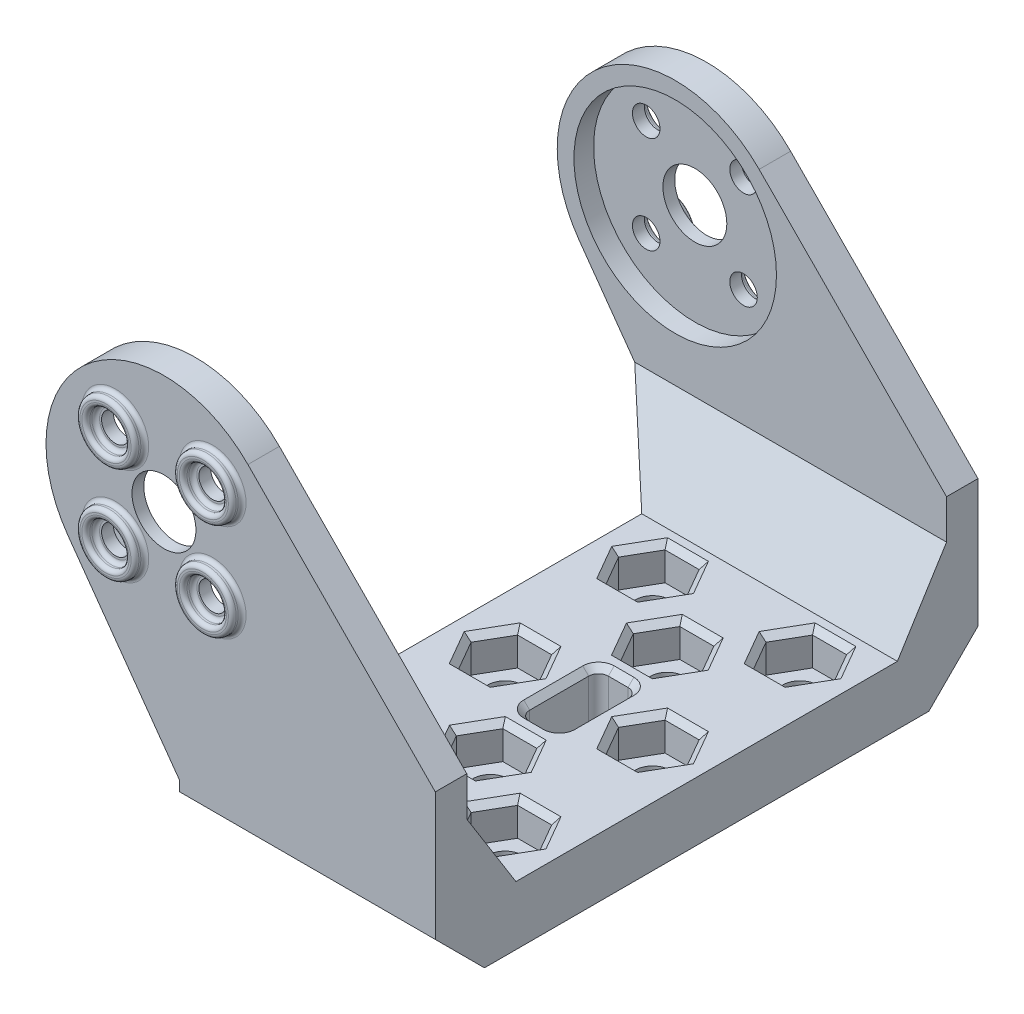
SolidWorks part; units mm, degrees
ref_plane "Спереди" through (0, 0, 0) normal (0, 0, 1) x (1, 0, 0)
ref_plane "Сверху" through (0, 0, 0) normal (0, 1, 0) x (1, 0, 0)
ref_plane "Справа" through (0, 0, 0) normal (1, 0, 0) x (0, 0, -1)
sketch "Эскиз1" plane through (0, 0, 0) normal (0, 0, 1) x (1, 0, 0)
  line L0 (0, 0) -> (0, -64.8775) construction
  line L1 (-4.9497, 4.9497) -> (4.9497, 4.9497) construction
  line L2 (-4.9497, 4.9497) -> (-4.9497, -4.9497) construction
  line L3 (-4.9497, -4.9497) -> (4.9497, -4.9497) construction
  line L4 (4.9497, 4.9497) -> (4.9497, -4.9497) construction
  line L5 (-4.9497, 4.9497) -> (4.9497, -4.9497) construction
  line L6 (-4.9497, -4.9497) -> (4.9497, 4.9497) construction
  line L7 (0, -64.8775) -> (14.6, -64.8775) construction
  line L8 (24.6, -34.8775) -> (4.6, -34.8775) construction
  line L9 (24.6, -34.8775) -> (24.6, -74.8775) construction
  line L10 (4.6, -34.8775) -> (4.6, -74.8775) construction
  line L11 (4.6, -74.8775) -> (24.6, -74.8775) construction
  line L12 (14.6, -73.302) -> (14.6, -29.9429) construction
  line L13 (2.6, -28.8775) -> (26.6, -28.8775) construction
  line L14 (2.6, -28.8775) -> (2.6, -48.8775) construction
  line L15 (2.6, -48.8775) -> (26.6, -48.8775) construction
  line L16 (26.6, -28.8775) -> (26.6, -48.8775) construction
  line L17 (1.6, -28.8775) -> (1.6, -22.8775)
  line L18 (1.6, -28.8775) -> (27.6, -28.8775)
  line L19 (27.6, -28.8775) -> (27.6, -10.8775)
  line L20 (27.6, -10.8775) -> (8.5399, 8.4303)
  line L21 (1.6, -22.8775) -> (-9.7631, -6.9772)
  circle A0 centre (0, 0) radius 3.25
  circle A1 centre (-4.9497, 4.9497) radius 1.4
  circle A2 centre (4.9497, 4.9497) radius 1.4
  circle A3 centre (4.9497, -4.9497) radius 1.4
  circle A4 centre (-4.9497, -4.9497) radius 1.4
  circle A5 centre (0, 0) radius 10 construction
  circle A6 centre (7.1, -37.3775) radius 1 construction
  arc A7 (8.5399, 8.4303) -> (-9.7631, -6.9772) centre (0, 0) ccw
  circle A11 centre (14.6, -64.8775) radius 10 construction
  circle A12 centre (14.6, -37.1275) radius 1 construction
  circle A13 centre (21.6, -44.1275) radius 1 construction
  circle A14 centre (7.6, -44.1275) radius 1 construction
  point P3 (0, 0)
  point P50 (32.6, -34.8775)
  dimension "D1" = 6.5
  dimension "D3" = 2.8
  dimension "D6" = 20
  dimension "D9" = 2
  dimension "D15" = 6
  dimension "D16" = 10
  dimension "D17" = 14
  dimension "D21" = 26
  dimension "D22" = 6
  dimension "D20" = 24
  dimension "D2" = 14
  dimension "D4" = 66.5
  dimension "D5" = 14.6
  dimension "D7" = 27.5
  dimension "D8" = 7.5
  dimension "D10" = 18
  dimension "D12" = 30
  dimension "D13" = 20
  dimension "D14" = 40
  dimension "D18" = 24
  dimension "D19" = 7
  dimension "D24" = 27.75
  dimension "D25" = 7
  dimension "D26" = 7
extrude "Бобышка-Вытянуть1" add sketch "Эскиз1" along normal blind 3.2
sketch "Эскиз2" plane through (0, 0, 3.2) normal (0, 0, 1) x (1, 0, 0)
  line L1 (27.6, -28.8775) -> (1.6, -28.8775)
  line L2 (27.6, -28.8775) -> (27.6, -22.8775)
  line L3 (27.6, -22.8775) -> (1.6, -22.8775)
  line L4 (1.6, -28.8775) -> (1.6, -22.8775)
extrude "Бобышка-Вытянуть2" add sketch "Эскиз2" along normal blind 48.8
sketch "Эскиз3" plane through (0, 0, 52) normal (0, 0, 1) x (1, 0, 0)
  line L5 (1.6, -28.8775) -> (27.6, -28.8775)
  line L6 (1.6, -22.8775) -> (1.6, -28.8775)
  line L7 (-9.7631, -6.9772) -> (1.6, -22.8775)
  line L8 (27.6, -10.8775) -> (8.5399, 8.4303)
  line L9 (27.6, -28.8775) -> (27.6, -10.8775)
  line L10 (1.6, -28.8775) -> (27.6, -28.8775)
  line L11 (1.6, -22.8775) -> (1.6, -28.8775)
  line L12 (-9.7631, -6.9772) -> (1.6, -22.8775)
  line L13 (27.6, -10.8775) -> (8.5399, 8.4303)
  line L14 (27.6, -28.8775) -> (27.6, -10.8775)
  circle A0 centre (-4.9497, 4.9497) radius 1.4 construction
  arc A1 (8.5399, 8.4303) -> (-9.7631, -6.9772) centre (0, 0) ccw
  arc A2 (8.5399, 8.4303) -> (-9.7631, -6.9772) centre (0, 0) ccw
  circle A3 centre (0, 0) radius 3.25 construction
  circle A4 centre (-4.9497, -4.9497) radius 1.4 construction
  circle A5 centre (4.9497, -4.9497) radius 1.4 construction
  circle A6 centre (4.9497, 4.9497) radius 1.4 construction
  circle A7 centre (-4.9497, 4.9497) radius 1.4
  circle A8 centre (0, 0) radius 3.25
  circle A9 centre (-4.9497, -4.9497) radius 1.4
  circle A10 centre (4.9497, -4.9497) radius 1.4
  circle A11 centre (4.9497, 4.9497) radius 1.4
  dimension "D1" = 0
extrude "Бобышка-Вытянуть3" add sketch "Эскиз3" along normal blind 3.2
sketch "Эскиз4" plane through (0, 0, 3.2) normal (0, 0, 1) x (1, 0, 0)
  circle A0 centre (0, 0) radius 10.3
  dimension "D1" = 20.6
extrude "Вырез-Вытянуть1" cut sketch "Эскиз4" against normal blind 2
sketch "Эскиз5" plane through (0, 0, 52) normal (0, 0, -1) x (-1, 0, 0)
  circle A0 centre (0, 0) radius 10.3 construction
  circle A1 centre (0, 0) radius 10.3
extrude "Вырез-Вытянуть2" cut sketch "Эскиз5" against normal blind 2
chamfer "Фаска1" distance 5 angle 45 2 edges at (14.6, -28.8775, 0) (14.6, -28.8775, 55.2)
sketch "Эскиз6" plane through (0, 0, 55.2) normal (0, 0, 1) x (1, 0, 0)
  circle A0 centre (-4.9497, 4.9497) radius 2
  circle A1 centre (-4.9497, 4.9497) radius 3
  circle A2 centre (-4.9497, -4.9497) radius 2
  circle A3 centre (4.9497, -4.9497) radius 2
  circle A4 centre (4.9497, -4.9497) radius 3
  circle A5 centre (-4.9497, -4.9497) radius 3
  circle A6 centre (4.9497, 4.9497) radius 2
  circle A7 centre (4.9497, 4.9497) radius 3
  dimension "D1" = 4
  dimension "D2" = 1
extrude "Бобышка-Вытянуть4" add sketch "Эскиз6" along normal blind 1
sketch "Эскиз7" plane through (0, 0, 0) normal (0, 0, -1) x (-1, 0, 0)
  circle A0 centre (4.9497, -4.9497) radius 3 construction
  circle A1 centre (4.9497, 4.9497) radius 3 construction
  circle A2 centre (-4.9497, 4.9497) radius 3 construction
  circle A3 centre (-4.9497, -4.9497) radius 3 construction
  circle A4 centre (4.9497, -4.9497) radius 3
  circle A5 centre (4.9497, 4.9497) radius 3
  circle A6 centre (-4.9497, 4.9497) radius 3
  circle A7 centre (-4.9497, -4.9497) radius 3
  circle A8 centre (4.9497, 4.9497) radius 2 construction
  circle A9 centre (-4.9497, 4.9497) radius 2 construction
  circle A10 centre (-4.9497, -4.9497) radius 2 construction
  circle A11 centre (4.9497, -4.9497) radius 2 construction
  circle A12 centre (4.9497, 4.9497) radius 2
  circle A13 centre (-4.9497, 4.9497) radius 2
  circle A14 centre (-4.9497, -4.9497) radius 2
  circle A15 centre (4.9497, -4.9497) radius 2
extrude "Бобышка-Вытянуть5" add sketch "Эскиз7" along normal blind 1
fillet "Скругление1" radius 0.4 32 edges at (7.9497, -4.9497, 0) (-1.9497, -4.9497, 0) (1.9497, -4.9497, -1) (2.9497, -4.9497, 0) (2.9497, -4.9497, -1) (-7.9497, -4.9497, -1) (-6.9497, -4.9497, 0) (-6.9497, -4.9497, -1) (-6.9497, 4.9497, 0) (-6.9497, 4.9497, -1) (-1.9497, 4.9497, 0) (-7.9497, 4.9497, -1) (7.9497, 4.9497, 0) (2.9497, 4.9497, 0) (2.9497, 4.9497, -1) (1.9497, 4.9497, -1) (-1.9497, 4.9497, 55.2) (-1.9497, -4.9497, 55.2) (7.9497, -4.9497, 55.2) (7.9497, 4.9497, 55.2) (-1.9497, 4.9497, 56.2) (-2.9497, 4.9497, 55.2) (-2.9497, 4.9497, 56.2) (6.9497, 4.9497, 55.2) (6.9497, 4.9497, 56.2) (7.9497, 4.9497, 56.2) (7.9497, -4.9497, 56.2) (-1.9497, -4.9497, 56.2) (-2.9497, -4.9497, 55.2) (-2.9497, -4.9497, 56.2) (6.9497, -4.9497, 55.2) (6.9497, -4.9497, 56.2)
sketch "Эскиз8" plane through (0, -22.8775, 0) normal (0, 1, 0) x (1, 0, 0)
  line L0 (-9.3037, -27.6) -> (38.3675, -27.6) construction
  line L1 (7.1, -12.6) -> (22.1, -12.6) construction
  line L2 (7.1, -12.6) -> (7.1, -42.6) construction
  line L3 (7.1, -42.6) -> (22.1, -42.6) construction
  line L4 (22.1, -12.6) -> (22.1, -42.6) construction
  line L5 (14.6, -8.2) -> (14.6, -47) construction
  line L7 (13.6, -31.6) -> (15.6, -31.6)
  line L8 (12.6, -30.6) -> (12.6, -24.6)
  line L9 (13.6, -23.6) -> (15.6, -23.6)
  line L10 (16.6, -30.6) -> (16.6, -24.6)
  line L11 (12.6, -31.6) -> (16.6, -23.6) construction
  line L12 (12.6, -23.6) -> (16.6, -31.6) construction
  circle A0 centre (7.1, -12.6) radius 1.75
  circle A1 centre (22.1, -12.6) radius 1.75
  circle A2 centre (22.1, -42.6) radius 1.75
  circle A3 centre (7.1, -42.6) radius 1.75
  circle A4 centre (22.1, -27.6) radius 1.75
  circle A5 centre (7.1, -27.6) radius 1.75
  circle A6 centre (14.6, -18.6) radius 1.75
  circle A7 centre (14.6, -36.6) radius 1.75
  arc A8 (15.6, -31.6) -> (16.6, -30.6) centre (15.6, -30.6) ccw
  arc A9 (13.6, -31.6) -> (12.6, -30.6) centre (13.6, -30.6) cw
  arc A10 (12.6, -24.6) -> (13.6, -23.6) centre (13.6, -24.6) cw
  arc A11 (16.6, -24.6) -> (15.6, -23.6) centre (15.6, -24.6) ccw
  point P20 (14.6, -27.6)
  dimension "D3" = 3.5
  dimension "D7" = 1
  dimension "D1" = 15
  dimension "D2" = 30
  dimension "D4" = 6
  dimension "D5" = 4
  dimension "D6" = 8
extrude "Вырез-Вытянуть3" cut sketch "Эскиз8" against normal up to surface (6 mm away) up to face at (14.6, -28.8775, 27.6)
sketch "Эскиз9" plane through (0, -22.8775, 0) normal (0, 1, 0) x (1, 0, 0)
  line L1 (10.5641, -12.6) -> (8.8321, -9.6)
  line L2 (8.8321, -9.6) -> (5.3679, -9.6)
  line L3 (5.3679, -9.6) -> (3.6359, -12.6)
  line L4 (3.6359, -12.6) -> (5.3679, -15.6)
  line L5 (5.3679, -15.6) -> (8.8321, -15.6)
  line L6 (8.8321, -15.6) -> (10.5641, -12.6)
  line L7 (18.6359, -12.6) -> (20.3679, -15.6)
  line L8 (20.3679, -15.6) -> (23.8321, -15.6)
  line L9 (23.8321, -15.6) -> (25.5641, -12.6)
  line L10 (25.5641, -12.6) -> (23.8321, -9.6)
  line L11 (23.8321, -9.6) -> (20.3679, -9.6)
  line L12 (20.3679, -9.6) -> (18.6359, -12.6)
  line L13 (18.0641, -18.6) -> (16.3321, -15.6)
  line L14 (16.3321, -15.6) -> (12.8679, -15.6)
  line L15 (12.8679, -15.6) -> (11.1359, -18.6)
  line L16 (11.1359, -18.6) -> (12.8679, -21.6)
  line L17 (12.8679, -21.6) -> (16.3321, -21.6)
  line L18 (16.3321, -21.6) -> (18.0641, -18.6)
  line L19 (10.5641, -27.6) -> (8.8321, -24.6)
  line L20 (8.8321, -24.6) -> (5.3679, -24.6)
  line L21 (5.3679, -24.6) -> (3.6359, -27.6)
  line L22 (3.6359, -27.6) -> (5.3679, -30.6)
  line L23 (5.3679, -30.6) -> (8.8321, -30.6)
  line L24 (8.8321, -30.6) -> (10.5641, -27.6)
  line L25 (18.6359, -27.6) -> (20.3679, -30.6)
  line L26 (20.3679, -30.6) -> (23.8321, -30.6)
  line L27 (23.8321, -30.6) -> (25.5641, -27.6)
  line L28 (25.5641, -27.6) -> (23.8321, -24.6)
  line L29 (23.8321, -24.6) -> (20.3679, -24.6)
  line L30 (20.3679, -24.6) -> (18.6359, -27.6)
  line L31 (18.0641, -36.6) -> (16.3321, -33.6)
  line L32 (16.3321, -33.6) -> (12.8679, -33.6)
  line L33 (12.8679, -33.6) -> (11.1359, -36.6)
  line L34 (11.1359, -36.6) -> (12.8679, -39.6)
  line L35 (12.8679, -39.6) -> (16.3321, -39.6)
  line L36 (16.3321, -39.6) -> (18.0641, -36.6)
  line L37 (18.6359, -42.6) -> (20.3679, -45.6)
  line L38 (20.3679, -45.6) -> (23.8321, -45.6)
  line L39 (23.8321, -45.6) -> (25.5641, -42.6)
  line L40 (25.5641, -42.6) -> (23.8321, -39.6)
  line L41 (23.8321, -39.6) -> (20.3679, -39.6)
  line L42 (20.3679, -39.6) -> (18.6359, -42.6)
  line L43 (10.5641, -42.6) -> (8.8321, -39.6)
  line L44 (8.8321, -39.6) -> (5.3679, -39.6)
  line L45 (5.3679, -39.6) -> (3.6359, -42.6)
  line L46 (3.6359, -42.6) -> (5.3679, -45.6)
  line L47 (5.3679, -45.6) -> (8.8321, -45.6)
  line L48 (8.8321, -45.6) -> (10.5641, -42.6)
  circle A0 centre (7.1, -12.6) radius 3 construction
  circle A1 centre (22.1, -12.6) radius 3 construction
  circle A2 centre (14.6, -18.6) radius 3 construction
  circle A3 centre (7.1, -27.6) radius 3 construction
  circle A4 centre (22.1, -27.6) radius 3 construction
  circle A5 centre (14.6, -36.6) radius 3 construction
  circle A6 centre (22.1, -42.6) radius 3 construction
  circle A7 centre (7.1, -42.6) radius 3 construction
  dimension "D1" = 6
extrude "Вырез-Вытянуть4" cut sketch "Эскиз9" against normal blind 3.5
chamfer "Фаска4" distance 8 distance2 5 1 edges
chamfer "Фаска5" distance 5 distance2 8 1 edges
chamfer "Фаска6" distance 0.6 angle 45 56 edges at (7.1, -22.8775, 45.6) (4.5019, -22.8775, 44.1) (4.5019, -22.8775, 41.1) (7.1, -22.8775, 39.6) (9.6981, -22.8775, 41.1) (9.6981, -22.8775, 44.1) (24.6981, -22.8775, 41.1) (22.1, -22.8775, 39.6) (19.5019, -22.8775, 41.1) (19.5019, -22.8775, 44.1) (22.1, -22.8775, 45.6) (24.6981, -22.8775, 44.1) (12.0019, -22.8775, 38.1) (14.6, -22.8775, 39.6) (17.1981, -22.8775, 38.1) (17.1981, -22.8775, 35.1) (14.6, -22.8775, 33.6) (12.0019, -22.8775, 35.1) (7.1, -22.8775, 30.6) (4.5019, -22.8775, 29.1) (4.5019, -22.8775, 26.1) (7.1, -22.8775, 24.6) (9.6981, -22.8775, 26.1) (9.6981, -22.8775, 29.1) (22.1, -22.8775, 15.6) (19.5019, -22.8775, 14.1) (19.5019, -22.8775, 11.1) (22.1, -22.8775, 9.6) (24.6981, -22.8775, 11.1) (24.6981, -22.8775, 14.1) (19.5019, -22.8775, 29.1) (22.1, -22.8775, 30.6) (24.6981, -22.8775, 29.1) (24.6981, -22.8775, 26.1) (22.1, -22.8775, 24.6) (19.5019, -22.8775, 26.1) (12.8929, -22.8775, 23.8929) (12.6, -22.8775, 27.6) (12.8929, -22.8775, 31.3071) (14.6, -22.8775, 31.6) (16.3071, -22.8775, 31.3071) (16.6, -22.8775, 27.6) (16.3071, -22.8775, 23.8929) (14.6, -22.8775, 23.6) (12.0019, -22.8775, 20.1) (14.6, -22.8775, 21.6) (17.1981, -22.8775, 20.1) (17.1981, -22.8775, 17.1) (14.6, -22.8775, 15.6) (12.0019, -22.8775, 17.1) (7.1, -22.8775, 15.6) (4.5019, -22.8775, 14.1) (4.5019, -22.8775, 11.1) (7.1, -22.8775, 9.6) (9.6981, -22.8775, 11.1) (9.6981, -22.8775, 14.1)
